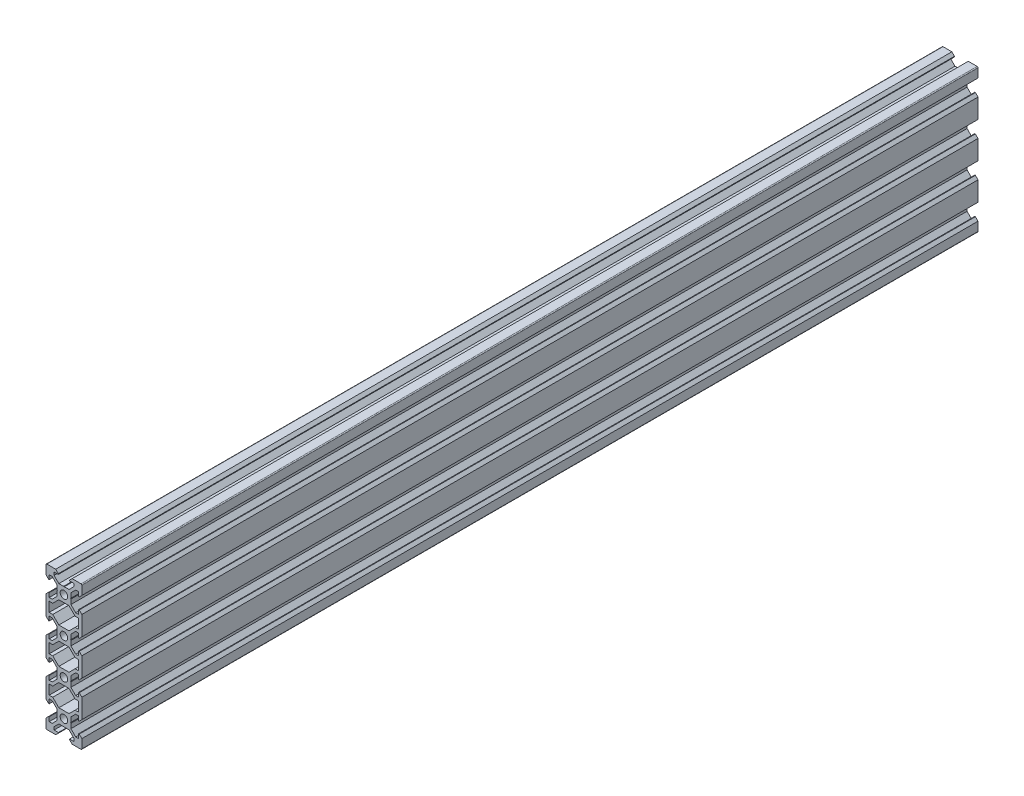
SolidWorks part; units mm, degrees
ref_plane "Front Plane" through (0, 0, 0) normal (0, 0, 1) x (1, 0, 0)
ref_plane "Top Plane" through (0, 0, 0) normal (0, 1, 0) x (1, 0, 0)
ref_plane "Right Plane" through (0, 0, 0) normal (1, 0, 0) x (0, 0, -1)
sketch "Sketch1" plane through (0, 0, 0) normal (0, 0, 1) x (1, 0, 0)
  line B0 (-8.2, -52.7) -> (-6.2393, -52.7)
  line B1 (-6.2393, -52.7) -> (-2.8393, -56.1)
  line B2 (-2.8393, -56.1) -> (2.8393, -56.1)
  line B3 (6.2393, -52.7) -> (2.8393, -56.1)
  line B4 (8.2, -52.7) -> (6.2393, -52.7)
  line B5 (8.2, -52.7) -> (8.2, -47.3)
  line B6 (8.2, -47.3) -> (6.2393, -47.3)
  line B7 (6.2393, -47.3) -> (2.8393, -43.9)
  line B8 (-2.8393, -43.9) -> (2.8393, -43.9)
  line B9 (-6.2393, -47.3) -> (-2.8393, -43.9)
  line B10 (-8.2, -47.3) -> (-6.2393, -47.3)
  line B11 (-8.2, -52.7) -> (-8.2, -47.3)
  line B12 (-8.2, -32.7) -> (-6.2393, -32.7)
  line B13 (-6.2393, -32.7) -> (-2.8393, -36.1)
  line B14 (-2.8393, -36.1) -> (2.8393, -36.1)
  line B15 (6.2393, -32.7) -> (2.8393, -36.1)
  line B16 (8.2, -32.7) -> (6.2393, -32.7)
  line B17 (8.2, -32.7) -> (8.2, -27.3)
  line B18 (8.2, -27.3) -> (6.2393, -27.3)
  line B19 (6.2393, -27.3) -> (2.8393, -23.9)
  line B20 (-2.8393, -23.9) -> (2.8393, -23.9)
  line B21 (-6.2393, -27.3) -> (-2.8393, -23.9)
  line B22 (-8.2, -27.3) -> (-6.2393, -27.3)
  line B23 (-8.2, -32.7) -> (-8.2, -27.3)
  line B24 (-8.2, -12.7) -> (-6.2393, -12.7)
  line B25 (-6.2393, -12.7) -> (-2.8393, -16.1)
  line B26 (-2.8393, -16.1) -> (2.8393, -16.1)
  line B27 (6.2393, -12.7) -> (2.8393, -16.1)
  line B28 (8.2, -12.7) -> (6.2393, -12.7)
  line B29 (8.2, -12.7) -> (8.2, -7.3)
  line B30 (8.2, -7.3) -> (6.2393, -7.3)
  line B31 (6.2393, -7.3) -> (2.8393, -3.9)
  line B32 (-2.8393, -3.9) -> (2.8393, -3.9)
  line B33 (-6.2393, -7.3) -> (-2.8393, -3.9)
  line B34 (-8.2, -7.3) -> (-6.2393, -7.3)
  line B35 (-8.2, -12.7) -> (-8.2, -7.3)
  line B36 (3.69, 0) -> (3.9, -0.21)
  line B37 (3.9, -0.21) -> (3.9, -2.8393)
  line B38 (3.9, -2.8393) -> (6.5607, -5.5)
  line B39 (6.5607, -5.5) -> (8.2, -5.5)
  line B40 (8.2, -5.5) -> (8.2, -3.125)
  line B41 (8.2, -3.125) -> (8.545, -3.125)
  line B42 (8.545, -3.125) -> (10, -4.58)
  line B43 (10, -15.42) -> (10, -4.58)
  line B44 (8.545, -16.875) -> (10, -15.42)
  line B45 (8.2, -16.875) -> (8.545, -16.875)
  line B46 (8.2, -14.5) -> (8.2, -16.875)
  line B47 (6.5607, -14.5) -> (8.2, -14.5)
  line B48 (3.9, -17.1607) -> (6.5607, -14.5)
  line B49 (3.9, -19.79) -> (3.9, -17.1607)
  line B50 (3.69, -20) -> (3.9, -19.79)
  line B51 (3.69, -20) -> (3.9, -20.21)
  line B52 (3.9, -20.21) -> (3.9, -22.8393)
  line B53 (3.9, -22.8393) -> (6.5607, -25.5)
  line B54 (6.5607, -25.5) -> (8.2, -25.5)
  line B55 (8.2, -25.5) -> (8.2, -23.125)
  line B56 (8.2, -23.125) -> (8.545, -23.125)
  line B57 (8.545, -23.125) -> (10, -24.58)
  line B58 (10, -35.42) -> (10, -24.58)
  line B59 (8.545, -36.875) -> (10, -35.42)
  line B60 (8.2, -36.875) -> (8.545, -36.875)
  line B61 (8.2, -34.5) -> (8.2, -36.875)
  line B62 (6.5607, -34.5) -> (8.2, -34.5)
  line B63 (3.9, -37.1607) -> (6.5607, -34.5)
  line B64 (3.9, -39.79) -> (3.9, -37.1607)
  line B65 (3.69, -40) -> (3.9, -39.79)
  line B66 (3.69, -40) -> (3.9, -40.21)
  line B67 (3.9, -40.21) -> (3.9, -42.8393)
  line B68 (3.9, -42.8393) -> (6.5607, -45.5)
  line B69 (6.5607, -45.5) -> (8.2, -45.5)
  line B70 (8.2, -45.5) -> (8.2, -43.125)
  line B71 (8.2, -43.125) -> (8.545, -43.125)
  line B72 (8.545, -43.125) -> (10, -44.58)
  line B73 (10, -55.42) -> (10, -44.58)
  line B74 (8.545, -56.875) -> (10, -55.42)
  line B75 (8.2, -56.875) -> (8.545, -56.875)
  line B76 (8.2, -54.5) -> (8.2, -56.875)
  line B77 (6.5607, -54.5) -> (8.2, -54.5)
  line B78 (3.9, -57.1607) -> (6.5607, -54.5)
  line B79 (3.9, -59.79) -> (3.9, -57.1607)
  line B80 (3.69, -60) -> (3.9, -59.79)
  line B81 (3.69, -60) -> (3.9, -60.21)
  line B82 (3.9, -60.21) -> (3.9, -62.8393)
  line B83 (3.9, -62.8393) -> (6.5607, -65.5)
  line B84 (6.5607, -65.5) -> (8.2, -65.5)
  line B85 (8.2, -65.5) -> (8.2, -63.125)
  line B86 (8.2, -63.125) -> (8.545, -63.125)
  line B87 (8.545, -63.125) -> (10, -64.58)
  line B88 (10, -69.5) -> (10, -64.58)
  arc B89 (9.5, -70) -> (10, -69.5) centre (9.5, -69.5) ccw
  line B90 (9.5, -70) -> (4.58, -70)
  line B91 (3.125, -68.545) -> (4.58, -70)
  line B92 (3.125, -68.2) -> (3.125, -68.545)
  line B93 (5.5, -68.2) -> (3.125, -68.2)
  line B94 (5.5, -66.5607) -> (5.5, -68.2)
  line B95 (2.8393, -63.9) -> (5.5, -66.5607)
  line B96 (0.21, -63.9) -> (2.8393, -63.9)
  line B97 (0, -63.69) -> (0.21, -63.9)
  line B98 (0, -63.69) -> (-0.21, -63.9)
  line B99 (-0.21, -63.9) -> (-2.8393, -63.9)
  line B100 (-2.8393, -63.9) -> (-5.5, -66.5607)
  line B101 (-5.5, -66.5607) -> (-5.5, -68.2)
  line B102 (-5.5, -68.2) -> (-3.125, -68.2)
  line B103 (-3.125, -68.2) -> (-3.125, -68.545)
  line B104 (-3.125, -68.545) -> (-4.58, -70)
  line B105 (-4.58, -70) -> (-9.5, -70)
  arc B106 (-10, -69.5) -> (-9.5, -70) centre (-9.5, -69.5) ccw
  line B107 (-10, -69.5) -> (-10, -64.58)
  line B108 (-8.545, -63.125) -> (-10, -64.58)
  line B109 (-8.2, -63.125) -> (-8.545, -63.125)
  line B110 (-8.2, -65.5) -> (-8.2, -63.125)
  line B111 (-6.5607, -65.5) -> (-8.2, -65.5)
  line B112 (-3.9, -62.8393) -> (-6.5607, -65.5)
  line B113 (-3.9, -60.21) -> (-3.9, -62.8393)
  line B114 (-3.69, -60) -> (-3.9, -60.21)
  line B115 (-3.69, -60) -> (-3.9, -59.79)
  line B116 (-3.9, -59.79) -> (-3.9, -57.1607)
  line B117 (-3.9, -57.1607) -> (-6.5607, -54.5)
  line B118 (-6.5607, -54.5) -> (-8.2, -54.5)
  line B119 (-8.2, -54.5) -> (-8.2, -56.875)
  line B120 (-8.2, -56.875) -> (-8.545, -56.875)
  line B121 (-8.545, -56.875) -> (-10, -55.42)
  line B122 (-10, -55.42) -> (-10, -44.58)
  line B123 (-8.545, -43.125) -> (-10, -44.58)
  line B124 (-8.2, -43.125) -> (-8.545, -43.125)
  line B125 (-8.2, -45.5) -> (-8.2, -43.125)
  line B126 (-6.5607, -45.5) -> (-8.2, -45.5)
  line B127 (-3.9, -42.8393) -> (-6.5607, -45.5)
  line B128 (-3.9, -40.21) -> (-3.9, -42.8393)
  line B129 (-3.69, -40) -> (-3.9, -40.21)
  line B130 (-3.69, -40) -> (-3.9, -39.79)
  line B131 (-3.9, -39.79) -> (-3.9, -37.1607)
  line B132 (-3.9, -37.1607) -> (-6.5607, -34.5)
  line B133 (-6.5607, -34.5) -> (-8.2, -34.5)
  line B134 (-8.2, -34.5) -> (-8.2, -36.875)
  line B135 (-8.2, -36.875) -> (-8.545, -36.875)
  line B136 (-8.545, -36.875) -> (-10, -35.42)
  line B137 (-10, -35.42) -> (-10, -24.58)
  line B138 (-8.545, -23.125) -> (-10, -24.58)
  line B139 (-8.2, -23.125) -> (-8.545, -23.125)
  line B140 (-8.2, -25.5) -> (-8.2, -23.125)
  line B141 (-6.5607, -25.5) -> (-8.2, -25.5)
  line B142 (-3.9, -22.8393) -> (-6.5607, -25.5)
  line B143 (-3.9, -20.21) -> (-3.9, -22.8393)
  line B144 (-3.69, -20) -> (-3.9, -20.21)
  line B145 (-3.69, -20) -> (-3.9, -19.79)
  line B146 (-3.9, -19.79) -> (-3.9, -17.1607)
  line B147 (-3.9, -17.1607) -> (-6.5607, -14.5)
  line B148 (-6.5607, -14.5) -> (-8.2, -14.5)
  line B149 (-8.2, -14.5) -> (-8.2, -16.875)
  line B150 (-8.2, -16.875) -> (-8.545, -16.875)
  line B151 (-8.545, -16.875) -> (-10, -15.42)
  line B152 (-10, -15.42) -> (-10, -4.58)
  line B153 (-8.545, -3.125) -> (-10, -4.58)
  line B154 (-8.2, -3.125) -> (-8.545, -3.125)
  line B155 (-8.2, -5.5) -> (-8.2, -3.125)
  line B156 (-6.5607, -5.5) -> (-8.2, -5.5)
  line B157 (-3.9, -2.8393) -> (-6.5607, -5.5)
  line B158 (-3.9, -0.21) -> (-3.9, -2.8393)
  line B159 (-3.69, 0) -> (-3.9, -0.21)
  line B160 (-3.69, 0) -> (-3.9, 0.21)
  line B161 (-3.9, 0.21) -> (-3.9, 2.8393)
  line B162 (-3.9, 2.8393) -> (-6.5607, 5.5)
  line B163 (-6.5607, 5.5) -> (-8.2, 5.5)
  line B164 (-8.2, 5.5) -> (-8.2, 3.125)
  line B165 (-8.2, 3.125) -> (-8.545, 3.125)
  line B166 (-8.545, 3.125) -> (-10, 4.58)
  line B167 (-10, 4.58) -> (-10, 9.5)
  arc B168 (-9.5, 10) -> (-10, 9.5) centre (-9.5, 9.5) ccw
  line B169 (-4.58, 10) -> (-9.5, 10)
  line B170 (-3.125, 8.545) -> (-4.58, 10)
  line B171 (-3.125, 8.2) -> (-3.125, 8.545)
  line B172 (-5.5, 8.2) -> (-3.125, 8.2)
  line B173 (-5.5, 6.5607) -> (-5.5, 8.2)
  line B174 (-2.8393, 3.9) -> (-5.5, 6.5607)
  line B175 (-0.21, 3.9) -> (-2.8393, 3.9)
  line B176 (0, 3.69) -> (-0.21, 3.9)
  line B177 (0, 3.69) -> (0.21, 3.9)
  line B178 (0.21, 3.9) -> (2.8393, 3.9)
  line B179 (2.8393, 3.9) -> (5.5, 6.5607)
  line B180 (5.5, 6.5607) -> (5.5, 8.2)
  line B181 (5.5, 8.2) -> (3.125, 8.2)
  line B182 (3.125, 8.2) -> (3.125, 8.545)
  line B183 (3.125, 8.545) -> (4.58, 10)
  line B184 (9.5, 10) -> (4.58, 10)
  arc B185 (10, 9.5) -> (9.5, 10) centre (9.5, 9.5) ccw
  line B186 (10, 4.58) -> (10, 9.5)
  line B187 (8.545, 3.125) -> (10, 4.58)
  line B188 (8.2, 3.125) -> (8.545, 3.125)
  line B189 (8.2, 5.5) -> (8.2, 3.125)
  line B190 (6.5607, 5.5) -> (8.2, 5.5)
  line B191 (3.9, 2.8393) -> (6.5607, 5.5)
  line B192 (3.9, 0.21) -> (3.9, 2.8393)
  line B193 (3.69, 0) -> (3.9, 0.21)
  circle B194 centre (0, -60) radius 2.1
  circle B195 centre (0, 0) radius 2.1
  circle B196 centre (0, -20) radius 2.1
  circle B197 centre (0, -40) radius 2.1
sketch_block_instance "2080 - V-Slot-1"
sketch_block "2080 - V-Slot"
extrude "Boss-Extrude1" add sketch "Sketch1" along normal blind 500
